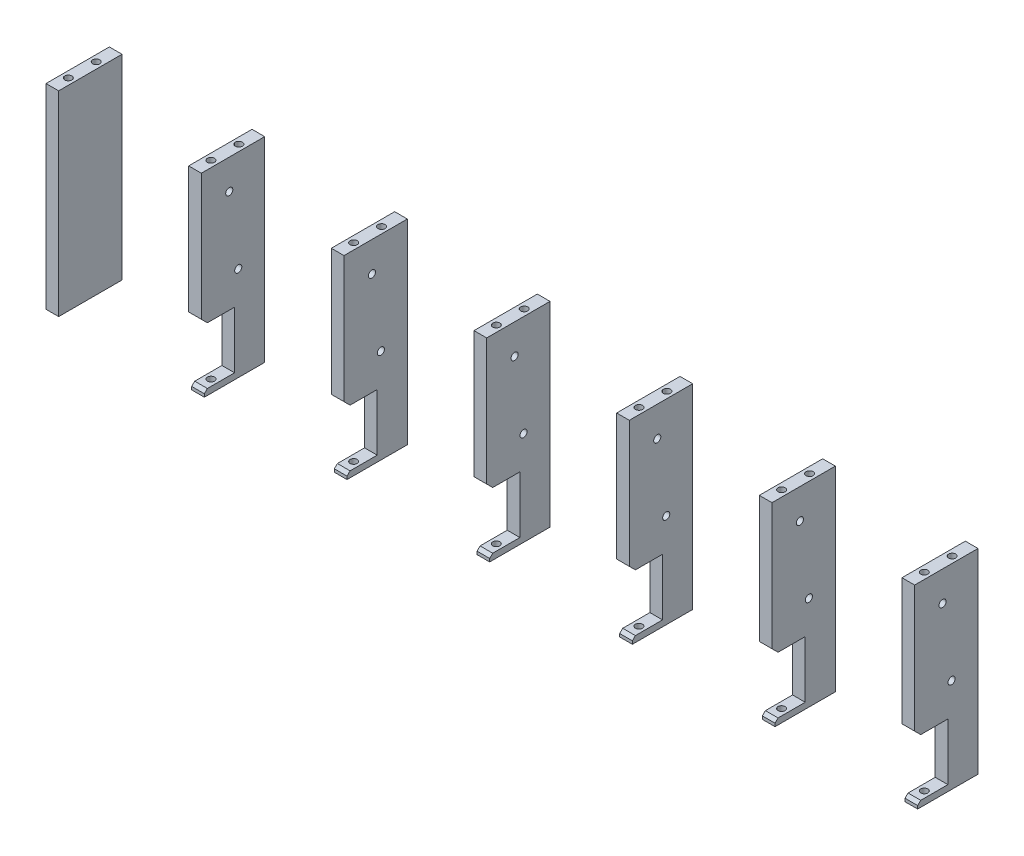
SolidWorks part; units mm, degrees
ref_plane "Front Plane" through (0, 0, 0) normal (0, 0, 1) x (1, 0, 0)
ref_plane "Top Plane" through (0, 0, 0) normal (0, 1, 0) x (1, 0, 0)
ref_plane "Right Plane" through (0, 0, 0) normal (1, 0, 0) x (0, 0, -1)
sketch "Sketch2" plane through (0, 0, -20) normal (0, 0, 1) x (1, 0, 0)
  line L0 (-69.0919, 2) -> (-69.0919, 1) construction
  line L1 (-69.0919, 99) -> (-62.7419, 99)
  line L2 (-69.0919, 99) -> (-69.0919, 1)
  line L3 (-69.0919, 1) -> (-62.7419, 1)
  line L4 (-62.7419, 99) -> (-62.7419, 1)
  line L5 (-62.7419, 1) -> (-62.7419, 2) construction
  line L6 (2.4081, 99) -> (8.7581, 99)
  line L7 (2.4081, 99) -> (2.4081, 1)
  line L8 (2.4081, 1) -> (8.7581, 1)
  line L9 (8.7581, 99) -> (8.7581, 1)
  line L10 (73.9081, 99) -> (80.2581, 99)
  line L11 (73.9081, 99) -> (73.9081, 1)
  line L12 (73.9081, 1) -> (80.2581, 1)
  line L13 (80.2581, 99) -> (80.2581, 1)
  line L14 (145.4081, 99) -> (151.7581, 99)
  line L15 (145.4081, 99) -> (145.4081, 1)
  line L16 (145.4081, 1) -> (151.7581, 1)
  line L17 (151.7581, 99) -> (151.7581, 1)
  line L18 (216.9081, 99) -> (223.2581, 99)
  line L19 (216.9081, 99) -> (216.9081, 1)
  line L20 (216.9081, 1) -> (223.2581, 1)
  line L21 (223.2581, 99) -> (223.2581, 1)
  line L22 (288.4081, 99) -> (294.7581, 99)
  line L23 (288.4081, 99) -> (288.4081, 1)
  line L24 (288.4081, 1) -> (294.7581, 1)
  line L25 (294.7581, 99) -> (294.7581, 1)
  line L26 (359.9081, 99) -> (366.2581, 99)
  line L27 (359.9081, 99) -> (359.9081, 1)
  line L28 (359.9081, 1) -> (366.2581, 1)
  line L29 (366.2581, 99) -> (366.2581, 1)
  dimension "D1" = 7
extrude "Boss-Extrude1" add sketch "Sketch2" against normal blind 31.75
sketch "Sketch3" plane through (0, 1, 0) normal (0, -1, 0) x (1, 0, 0)
  circle A0 centre (-65.9169, -28) radius 1.778
  circle A1 centre (-65.9169, -42) radius 1.778
  circle A2 centre (-65.9169, -28) radius 1.8987 construction
  circle A3 centre (-65.9169, -42) radius 1.8987 construction
  circle A4 centre (5.5831, -28) radius 1.778
  circle A5 centre (5.5831, -42) radius 1.778
  circle A6 centre (77.0831, -28) radius 1.778
  circle A7 centre (77.0831, -42) radius 1.778
  circle A8 centre (148.5831, -28) radius 1.778
  circle A9 centre (148.5831, -42) radius 1.778
  circle A10 centre (220.0831, -28) radius 1.778
  circle A11 centre (220.0831, -42) radius 1.778
  circle A12 centre (291.5831, -28) radius 1.778
  circle A13 centre (291.5831, -42) radius 1.778
  circle A14 centre (363.0831, -28) radius 1.778
  circle A15 centre (363.0831, -42) radius 1.778
  dimension "D1" = 7
extrude "Cut-Extrude1" cut sketch "Sketch3" against normal blind 10
sketch "Sketch4" plane through (0, 99, 0) normal (0, 1, 0) x (1, 0, 0)
  circle A0 centre (-65.9169, 42) radius 1.778
  circle A1 centre (-65.9169, 28) radius 1.778
  circle A2 centre (-65.9169, 42) radius 1.778 construction
  circle A3 centre (-65.9169, 28) radius 1.778 construction
  circle A4 centre (5.5831, 42) radius 1.778
  circle A5 centre (5.5831, 28) radius 1.778
  circle A6 centre (77.0831, 42) radius 1.778
  circle A7 centre (77.0831, 28) radius 1.778
  circle A8 centre (148.5831, 42) radius 1.778
  circle A9 centre (148.5831, 28) radius 1.778
  circle A10 centre (220.0831, 42) radius 1.778
  circle A11 centre (220.0831, 28) radius 1.778
  circle A12 centre (291.5831, 42) radius 1.778
  circle A13 centre (291.5831, 28) radius 1.778
  circle A14 centre (363.0831, 42) radius 1.778
  circle A15 centre (363.0831, 28) radius 1.778
  dimension "D1" = 7
extrude "Cut-Extrude2" cut sketch "Sketch4" against normal blind 10
sketch "Sketch5" plane through (2.4081, 0, 0) normal (-1, 0, 0) x (0, 0, 1)
  line L0 (-20, 99) -> (-20, 1) construction
  line L1 (-23.0414, 32.5414) -> (-20, 32.5414) construction
  line L2 (-20, 32.5414) -> (-20, 4.0414)
  line L3 (-20, 4.0414) -> (-23.0414, 4.0414) construction
  line L4 (-36.6539, 32.5414) -> (-36.6539, 4.0414)
  line L5 (-21.5207, 2.5207) -> (-20, 1) construction
  line L6 (-20, 1) -> (-20, 4.0414)
  line L7 (-23.0414, 4.0414) -> (-36.6539, 4.0414)
  line L8 (-23.0414, 32.5414) -> (-20, 35.5829)
  line L9 (-20, 35.5829) -> (-20, 32.5414)
  line L10 (-23.0414, 32.5414) -> (-36.6539, 32.5414)
  line L11 (-21.5207, 2.5207) -> (-21.5207, 1)
  line L12 (-21.5207, 2.5207) -> (-23.0414, 4.0414)
  line L13 (-21.5207, 1) -> (-20, 1)
extrude "Cut-Extrude3" cut sketch "Sketch5" against normal through all
sketch "Sketch6" plane through (2.4081, 0, 0) normal (-1, 0, 0) x (0, 0, 1)
  circle A0 centre (-38.5, 48.25) radius 1.778
  circle A1 centre (-34, 84) radius 1.778
extrude "Cut-Extrude4" cut sketch "Sketch6" against normal through all
